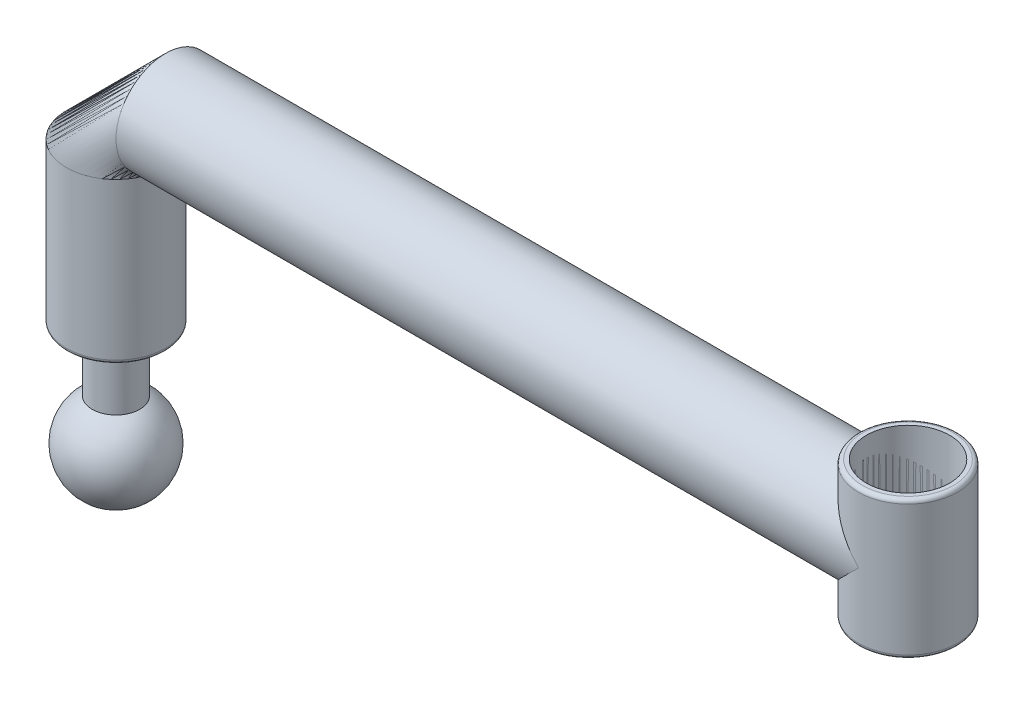
SolidWorks part; units mm, degrees
ref_plane "前基準面" through (0, 0, 0) normal (0, 0, 1) x (1, 0, 0)
ref_plane "上基準面" through (0, 0, 0) normal (0, 1, 0) x (1, 0, 0)
ref_plane "右基準面" through (0, 0, 0) normal (1, 0, 0) x (0, 0, -1)
sketch "草圖1" plane through (0, 0, 0) normal (0, 0, 1) x (1, 0, 0)
  line L0 (0, 12) -> (0, -12)
  arc A0 (0, -12) -> (0, 12) centre (0, 0) ccw
  dimension "D1" = 12
revolve "旋轉1" add sketch "草圖1" angle 360 about L0
sketch "草圖2" plane through (0, 0, 0) normal (0, 1, 0) x (1, 0, 0)
  circle A0 centre (0, 0) radius 6
  dimension "D1" = 12
extrude "填料-伸長1" add sketch "草圖2" along normal blind 26
sketch "草圖3" plane through (0, 26, 0) normal (0, 1, 0) x (1, 0, 0)
  circle A0 centre (0, 0) radius 12.5
  dimension "D1" = 25
sketch "草圖4" plane through (0, 0, 0) normal (0, 0, 1) x (1, 0, 0)
  line L0 (0, 26) -> (0, 66.5)
  line L1 (12.5, 79) -> (200, 79)
  line L2 (200, 79) -> (200, 61.5)
  arc A0 (0, 66.5) -> (12.5, 79) centre (12.5, 66.5) cw
  point P0 (0, 26)
  dimension "D1" = 12.5
  dimension "D2" = 200
  dimension "D4" = 17.5
  dimension "D5" = 53
sweep "掃出1" add profiles "草圖3" path "草圖4"
sketch "草圖5" plane through (0, 0, 0) normal (0, 0, 1) x (1, 0, 0)
  line L1 (200, 61.5) -> (200, 79)
  line L2 (200, 66.5) -> (200, 91.5) construction
  line L3 (200, 79) -> (200, 96.5)
  dimension "D1" = 17.5
  dimension "D2" = 17.5
ref_plane "平面1" through (0, 96.5, 0) normal (0, 1, 0) x (1, 0, 0)
sketch "草圖6" plane through (0, 96.5, 0) normal (0, 1, 0) x (1, 0, 0)
  line L0 (200, -12.5) -> (200, 12.5) construction
  circle A0 centre (200, 0) radius 12.5
  dimension "D1" = 25
sweep "掃出2" add profiles "草圖6" path "草圖5"
shell "薄殼1" thickness 2
sketch "草圖7" plane through (0, 63.5, 0) normal (0, 1, 0) x (1, 0, 0)
  circle A1 centre (200, 0) radius 10.5
  circle A2 centre (200, 0) radius 10.5
  dimension "D1" = 0
extrude "除料-伸長1" cut sketch "草圖7" along normal through all
ref_plane "平面2" through (0, 0, 0) normal (0, 0, 1) x (1, 0, 0)
ref_plane "平面3" through (0, 0, 0) normal (1, 0, 0) x (0, 0, -1)
fillet "圓角1" radius 1 1 edges at (0, 26, 12.5)
fillet "圓角2" radius 1 2 edges at (200, 96.5, 12.5) (200, 61.5, 12.5)
sketch "草圖8" plane through (0, 0, 0) normal (0, 0, 1) x (1, 0, 0)
  point P0 (0, 0)
